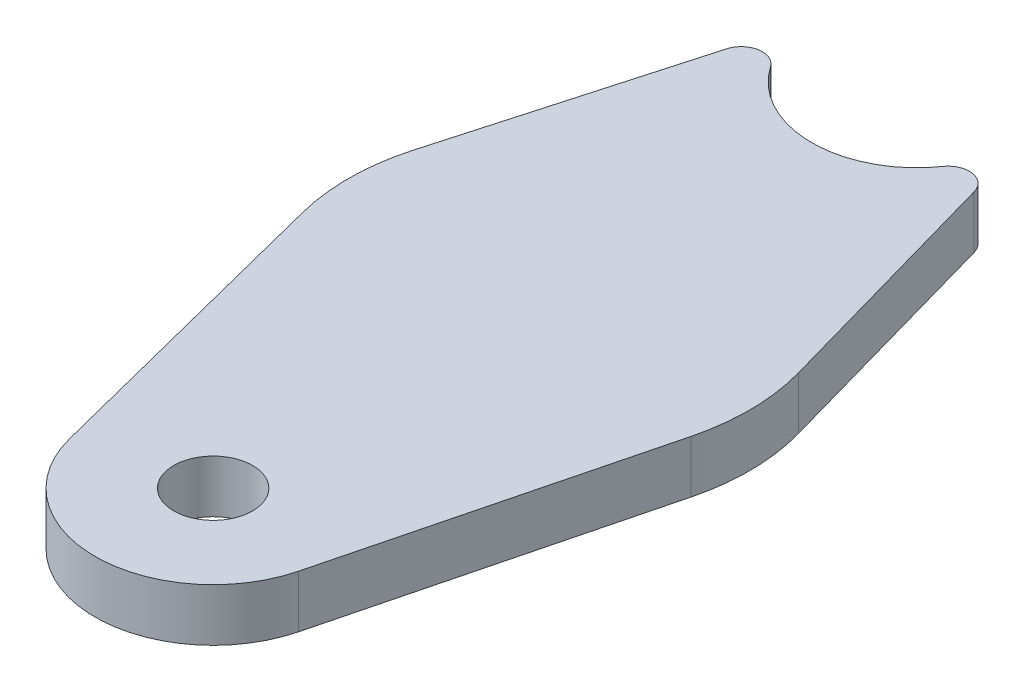
SolidWorks part; units mm, degrees
ref_plane "Front Plane" through (0, 0, 0) normal (0, 0, 1) x (1, 0, 0)
ref_plane "Top Plane" through (0, 0, 0) normal (0, 1, 0) x (1, 0, 0)
ref_plane "Right Plane" through (0, 0, 0) normal (1, 0, 0) x (0, 0, -1)
sketch3d "reference sketch"
  line L10 (473.0711, 15.875, 204.6054) -> (-3.7085, 15.875, 29.2622) construction
  line L11 (0, -9.525, 544.3909) -> (513.1803, 15.875, 142.9509) construction
  line L12 (0, -9.525, 544.3909) -> (0, 15.875, -54.4099) construction
  line L13 (0, 340.475, -54.4099) -> (0, -9.525, -54.4099) construction
  line L14 (502.6591, 111.456, 171.5592) -> (0, -9.525, -54.4099) construction
  line L15 (0, -9.525, -54.4099) -> (844.6883, -9.525, 256.2374) construction
sketch "Sketch13" plane through (0, 0, 0) normal (0, 1, 0) x (1, 0, 0)
  line L0 (12.7, 54.4099) -> (25.1378, 10.2862)
  line L1 (-12.7, 54.4099) -> (12.7, 54.4099)
  line L2 (25.1378, 10.2862) -> (13.8474, -34.1449)
  line L4 (0, 54.4099) -> (0, -30.6261) construction
  line L5 (-25.1378, 10.2862) -> (-13.8474, -34.1449)
  line L6 (-12.7, 54.4099) -> (-25.1378, 10.2862)
  line L7 (12.7, 54.4099) -> (13.8474, -34.1449) construction
  line L9 (0, -544.3909) -> (0, 54.4099) construction
  line L10 (473.0711, -204.6054) -> (-3.7085, -29.2622) construction
  arc A0 (13.8474, -34.1449) -> (-13.8474, -34.1449) centre (0, -30.6261) cw
  circle A2 centre (0, -30.6261) radius 4.7625
  arc A3 (-12.7, 54.4099) -> (12.7, 54.4099) centre (0, 54.4099) ccw construction
  point P6 (0, 0)
  point P7 (13.6787, -34.7525)
  point P10 (25.1375, 10.2864)
  point P14 (12.6994, 54.2823)
  point P17 (13.8678, -34.0638)
  point P18 (0, 54.4099)
  dimension "D2" = 9.525
  dimension "D4" = 12.7
  dimension "D1" = 9.525
  dimension "D3" = 15
  dimension "D5" = 25.4
extrude "Boss-Extrude1" add sketch "Sketch13" along normal blind 6.35
sketch "Sketch14" plane through (0, 0, 0) normal (0, 1, 0) x (1, 0, 0)
  circle A1 centre (0, 54.4099) radius 12.7
  point P1 (-1.2416, 50.7068)
  dimension "D1" = 25.4
extrude "Cut-Extrude1" cut sketch "Sketch14" against normal through all both and the other way through all
fillet "Fillet1" radius 2.54 2 edges at (12.7, 3.175, -54.4099) (-12.7, 3.175, -54.4099)
fillet "Fillet2" radius 25.4 2 edges at (25.1378, 3.175, -10.2862) (-25.1378, 3.175, -10.2862)
equation "\"D1@Sketch13\"=\"D2@Sketch13\"*1"
